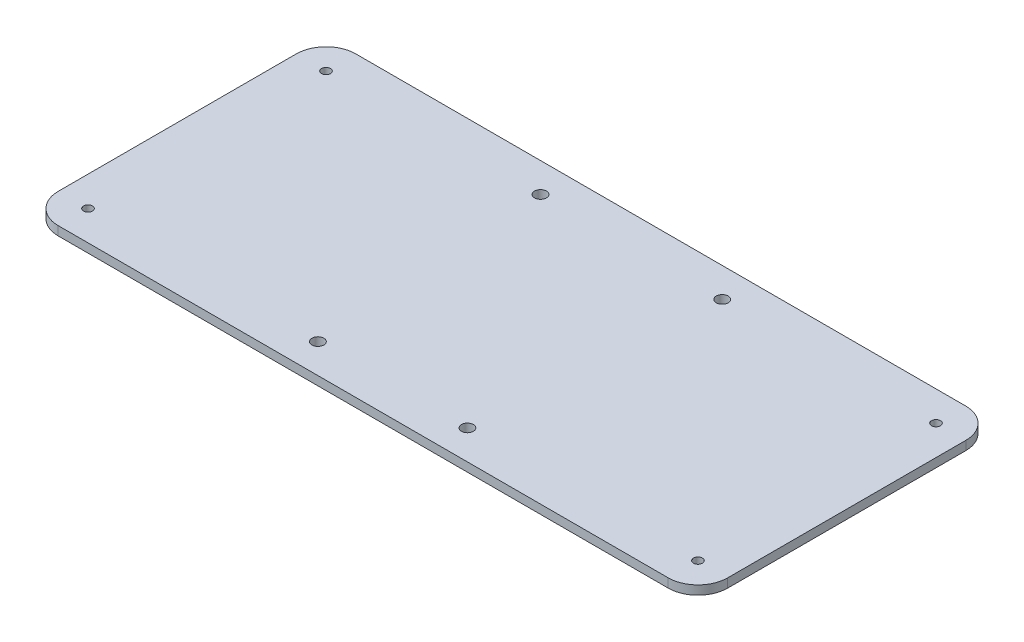
SolidWorks part; units mm, degrees
ref_plane "Front Plane" through (0, 0, 0) normal (0, 0, 1) x (1, 0, 0)
ref_plane "Top Plane" through (0, 0, 0) normal (0, 1, 0) x (1, 0, 0)
ref_plane "Right Plane" through (0, 0, 0) normal (1, 0, 0) x (0, 0, -1)
sketch "Sketch1" plane through (0, 0, 0) normal (0, 1, 0) x (1, 0, 0)
  line L0 (-30.535, 40.11) -> (30.535, 40.11) construction
  line L1 (-112.5, 50) -> (112.5, 50)
  line L2 (-112.5, 50) -> (-112.5, -50)
  line L3 (-112.5, -50) -> (112.5, -50)
  line L4 (112.5, 50) -> (112.5, -50)
  line L5 (-112.5, 50) -> (112.5, -50) construction
  line L6 (-112.5, -50) -> (112.5, 50) construction
  line L11 (0, 0) -> (0, 40.11) construction
  line L12 (-25.125, -40.11) -> (25.125, -40.11) construction
  line L13 (0, 0) -> (0, -40.11) construction
  line L14 (0, 40.11) -> (0, 50) construction
  line L15 (0, -40.11) -> (0, -50) construction
  circle A0 centre (-102.5, 40) radius 1.5
  circle A1 centre (102.5, 40) radius 1.5
  circle A2 centre (-102.5, -40) radius 1.5
  circle A3 centre (102.5, -40) radius 1.5
  circle A4 centre (-30.535, 40.11) radius 2
  circle A5 centre (30.535, 40.11) radius 2
  circle A6 centre (25.125, -40.11) radius 2
  circle A7 centre (-25.125, -40.11) radius 2
  point P8 (0, 0)
  dimension "D2" = 10
  dimension "D3" = 10
  dimension "D4" = 10
  dimension "D7" = 10
  dimension "D8" = 10
  dimension "D9" = 10
  dimension "D10" = 10
  dimension "D11" = 3
  dimension "D12" = 10
  dimension "D13" = 3
  dimension "D20" = 4
  dimension "D5" = 225
  dimension "D6" = 100
  dimension "D14" = 61.07
  dimension "D15" = 80.22
  dimension "D17" = 50.25
extrude "Boss-Extrude1" add sketch "Sketch1" along normal blind 3
fillet "Fillet1" radius 10 4 edges at (-112.5, 1.5, -50) (-112.5, 1.5, 50) (112.5, 1.5, -50) (112.5, 1.5, 50)
